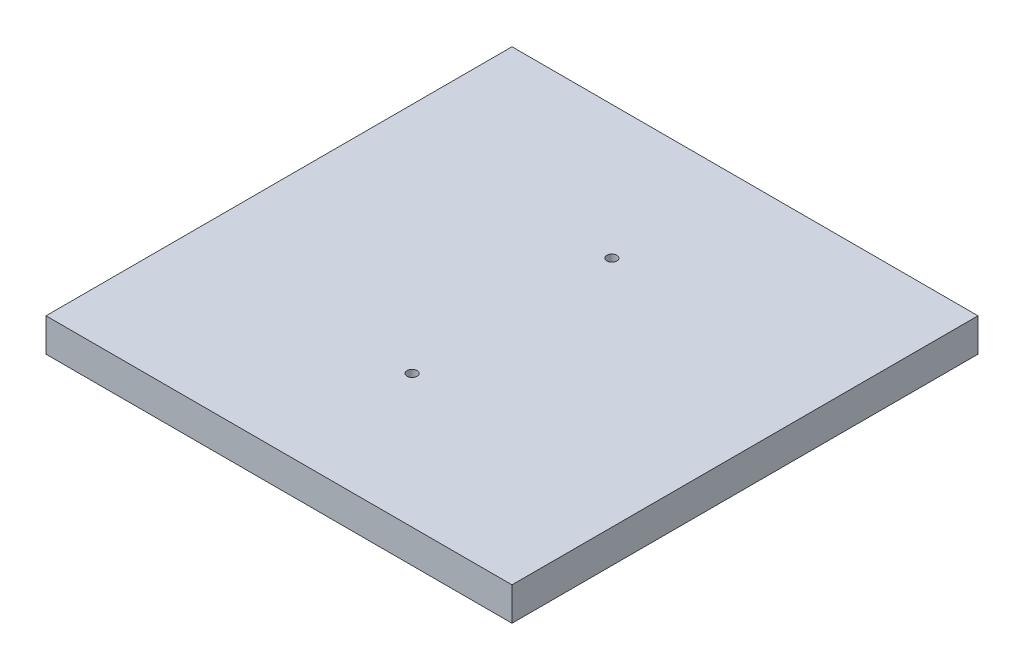
SolidWorks part; units mm, degrees
ref_plane "Front Plane" through (0, 0, 0) normal (0, 0, 1) x (1, 0, 0)
ref_plane "Top Plane" through (0, 0, 0) normal (0, 1, 0) x (1, 0, 0)
ref_plane "Right Plane" through (0, 0, 0) normal (1, 0, 0) x (0, 0, -1)
sketch "Sketch1" plane through (0, 0, 0) normal (0, 1, 0) x (1, 0, 0)
  line L1 (-35, -35) -> (35, -35)
  line L2 (-35, -35) -> (-35, 35)
  line L3 (-35, 35) -> (35, 35)
  line L4 (35, -35) -> (35, 35)
  line L5 (-35, -35) -> (35, 35) construction
  line L6 (-35, 35) -> (35, -35) construction
  point P0 (0, 0)
  dimension "D1" = 70
  dimension "D2" = 70
extrude "Boss-Extrude1" add sketch "Sketch1" against normal blind 5 contours L3 L4 L1 L2
sketch "Sketch7" plane through (0, 0, 0) normal (0, 1, 0) x (1, 0, 0)
  line L0 (-35, -35) -> (-35, 35) construction
  line L3 (-35, 0) -> (35, 0) construction
  line L4 (35, -35) -> (35, 35) construction
  circle A0 centre (0, 15) radius 0.75
  circle A1 centre (0, -15) radius 0.75
  point P8 (0, -15)
  dimension "D1" = 15
  dimension "D2" = 1.5
  dimension "D3" = 35
extrude "Cut-Extrude1" cut sketch "Sketch7" against normal through all
